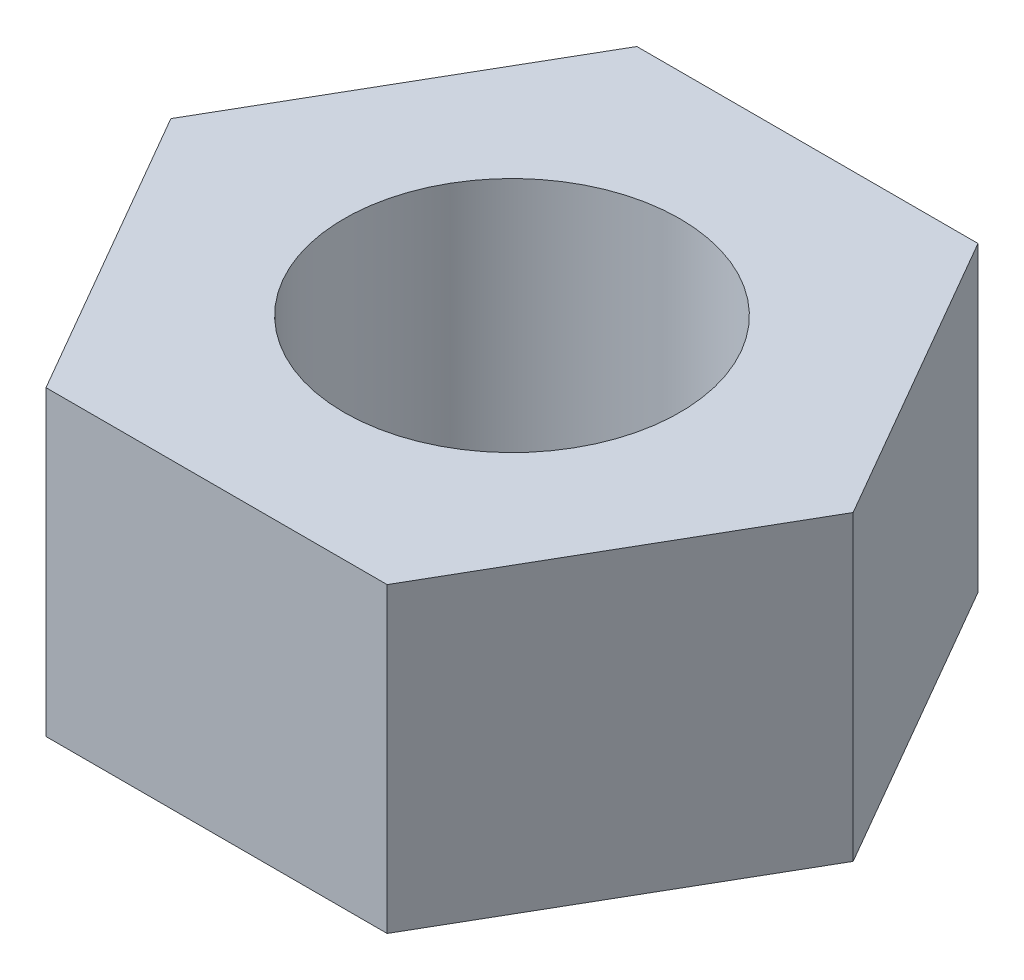
SolidWorks part; units mm, degrees
material "1.6523 (20NiCrMoS2-2)"
ref_plane "Front Plane" through (0, 0, 0) normal (0, 0, 1) x (1, 0, 0)
ref_plane "Top Plane" through (0, 0, 0) normal (0, 1, 0) x (1, 0, 0)
ref_plane "Right Plane" through (0, 0, 0) normal (1, 0, 0) x (0, 0, -1)
sketch "Sketch1" plane through (0, 0, 0) normal (0, 1, 0) x (1, 0, 0)
  line L1 (2.5403, -4.4) -> (5.0807, 0)
  line L2 (5.0807, 0) -> (2.5403, 4.4)
  line L3 (2.5403, 4.4) -> (-2.5403, 4.4)
  line L4 (-2.5403, 4.4) -> (-5.0807, 0)
  line L5 (-5.0807, 0) -> (-2.5403, -4.4)
  line L6 (-2.5403, -4.4) -> (2.5403, -4.4)
  circle A0 centre (0, 0) radius 2.5
  circle A1 centre (0, 0) radius 4.4 construction
  dimension "D1" = 8.8
  dimension "D2" = 5
extrude "Boss-Extrude1" add sketch "Sketch1" along normal blind 4.5
